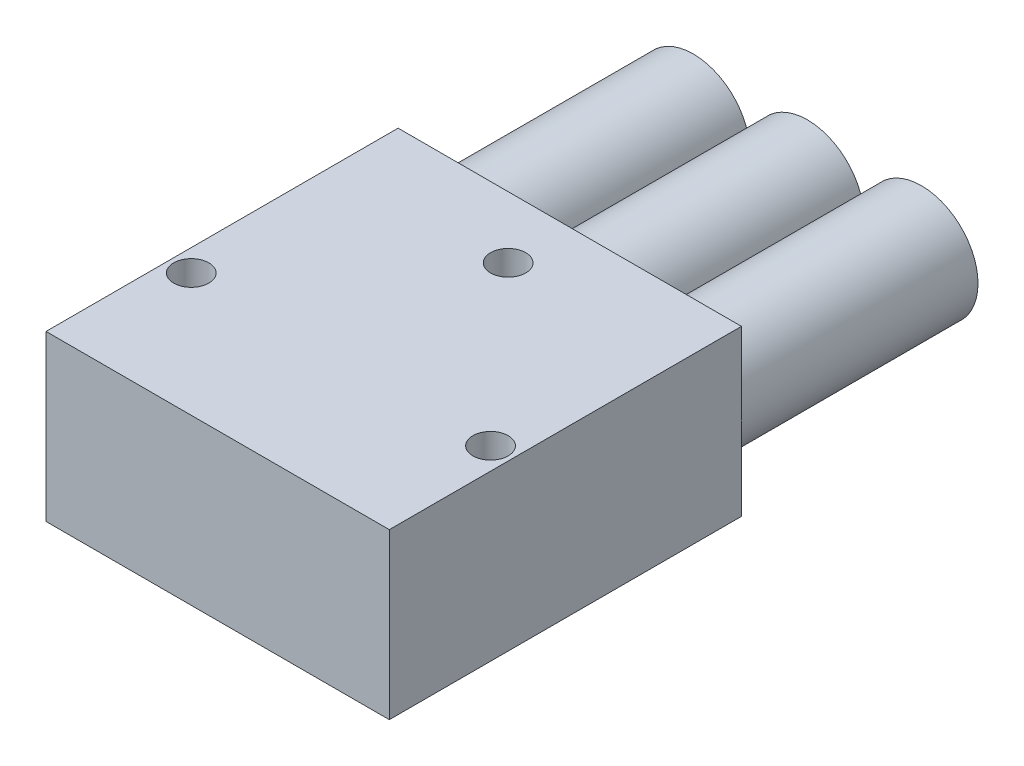
SolidWorks part; units mm, degrees
ref_plane "Front Plane" through (0, 0, 0) normal (0, 0, 1) x (1, 0, 0)
ref_plane "Top Plane" through (0, 0, 0) normal (0, 1, 0) x (1, 0, 0)
ref_plane "Right Plane" through (0, 0, 0) normal (1, 0, 0) x (0, 0, -1)
sketch "Sketch1" plane through (0, 0, 0) normal (0, 1, 0) x (1, 0, 0)
  line L1 (0, 0) -> (39, 0)
  line L2 (0, 0) -> (0, 40)
  line L3 (0, 40) -> (39, 40)
  line L4 (39, 0) -> (39, 40)
  dimension "D1" = 39
  dimension "D2" = 40
extrude "Boss-Extrude1" add sketch "Sketch1" along normal blind 18.7
sketch "Sketch2" plane through (0, 18.7, 0) normal (0, 1, 0) x (1, 0, 0)
  line L0 (2.5, 14) -> (36.5, 14) construction
  line L1 (36.5, 14) -> (19.5, 33) construction
  line L2 (19.5, 33) -> (2.5, 14) construction
  line L3 (2.5, 14) -> (0, 0) construction
  line L4 (36.5, 14) -> (39, 0) construction
  line L5 (0, 0) -> (39, 0) construction
  circle A0 centre (2.5, 14) radius 2
  circle A1 centre (36.5, 14) radius 2
  circle A2 centre (19.5, 33) radius 2
  point P12 (0, 0)
  dimension "D1" = 4
  dimension "D2" = 34
  dimension "D3" = 14
  dimension "D4" = 19
extrude "Cut-Extrude1" cut sketch "Sketch2" against normal blind 3
sketch "Sketch3" plane through (0, 0, -40) normal (0, 0, -1) x (-1, 0, 0)
  line L0 (-32.4585, 9.35) -> (-25.9171, 9.35) construction
  line L1 (-6.5415, 9.35) -> (-13.0829, 9.35) construction
  line L4 (-32.4585, 9.35) -> (-39, 9.35) construction
  line L5 (-39, 18.7) -> (-39, 0) construction
  line L6 (-6.5415, 9.35) -> (0, 9.35) construction
  line L7 (0, 18.7) -> (0, 0) construction
  line L8 (-13.0829, 9.35) -> (-19.5, 9.35) construction
  line L9 (-25.9171, 9.35) -> (-19.5, 9.35) construction
  circle A0 centre (-32.4585, 9.35) radius 6.4171
  circle A1 centre (-19.5, 9.35) radius 6.4171
  circle A2 centre (-6.5415, 9.35) radius 6.4171
  point P6 (0, 0)
  point P8 (-30.997, 9.35)
  point P9 (-31.8704, 9.35)
  dimension "D1" = 12.8342
extrude "Boss-Extrude4" add sketch "Sketch3" along normal blind 27
